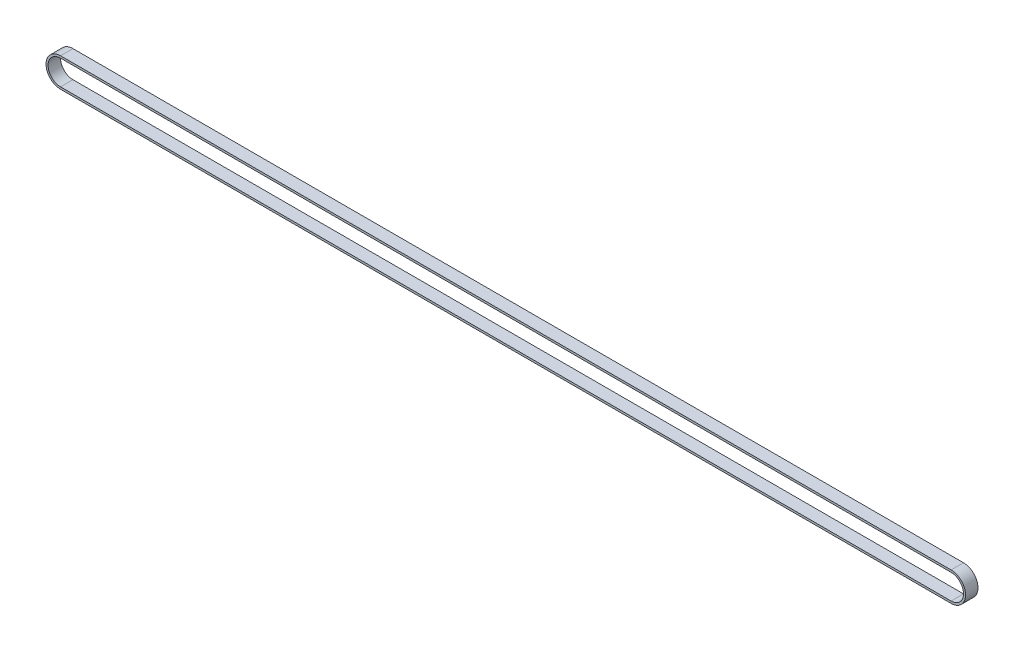
SolidWorks part; units mm, degrees
material "BUTYL"
ref_plane "Front Plane" through (0, 0, 0) normal (0, 0, 1) x (1, 0, 0)
ref_plane "Top Plane" through (0, 0, 0) normal (0, 1, 0) x (1, 0, 0)
ref_plane "Right Plane" through (0, 0, 0) normal (1, 0, 0) x (0, 0, -1)
sketch "Sketch1" plane through (0, 0, 0) normal (0, 0, 1) x (1, 0, 0)
  line L0 (0, 0) -> (430, 0) construction
  line L1 (0, 6) -> (430, 6)
  line L2 (0, -6) -> (430, -6)
  line L3 (0, 0) -> (430, 0) construction
  line L4 (0, 7) -> (430, 7)
  line L5 (0, -7) -> (430, -7)
  arc A0 (0, 6) -> (0, -6) centre (0, 0) ccw
  arc A1 (430, -6) -> (430, 6) centre (430, 0) ccw
  arc A2 (0, 7) -> (0, -7) centre (0, 0) ccw
  arc A3 (430, -7) -> (430, 7) centre (430, 0) ccw
  point P3 (215, 0)
  point P10 (215, 0)
  dimension "D1" = 430
  dimension "D2" = 12
  dimension "D3" = 1
extrude "Boss-Extrude1" add sketch "Sketch1" along normal blind 6
